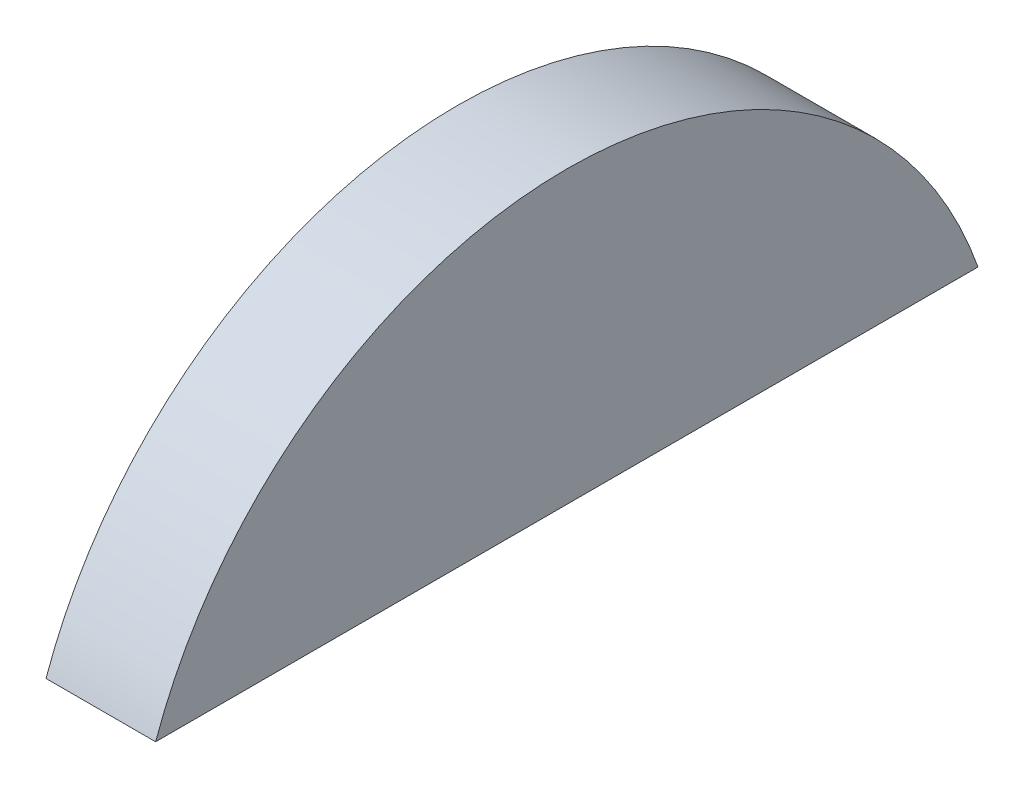
SolidWorks part; units mm, degrees
ref_plane "Front Plane" through (0, 0, 0) normal (0, 0, 1) x (1, 0, 0)
ref_plane "Top Plane" through (0, 0, 0) normal (0, 1, 0) x (1, 0, 0)
ref_plane "Right Plane" through (0, 0, 0) normal (1, 0, 0) x (0, 0, -1)
sketch "Sketch2" plane through (0, 0, 0) normal (1, 0, 0) x (0, 0, -1)
  line L0 (-19.05, 6.7478) -> (19.05, 6.7478)
  arc A0 (19.05, 6.7478) -> (-19.05, 6.7478) centre (0, 0) ccw
  point P4 (0, 20.2098)
  dimension "D1" = 13.462
  dimension "D2" = 38.1
extrude "Boss-Extrude2" add sketch "Sketch2" along normal blind 5.08
equation "\"TubeR\"= 0.8in"
equation "\"Foamcore\"= 0.2in"
equation "\"MDF\"= 0.2in"
equation "\"NutD\"= 0.2145in"
equation "\"NutH\"= 0.0915in"
equation "\"MountScrewL\"= 0.3in"
equation "\"MountScrewD\"= 3.6mm"
equation "\"D1@Boss-Extrude2\"=\"MDF\""
